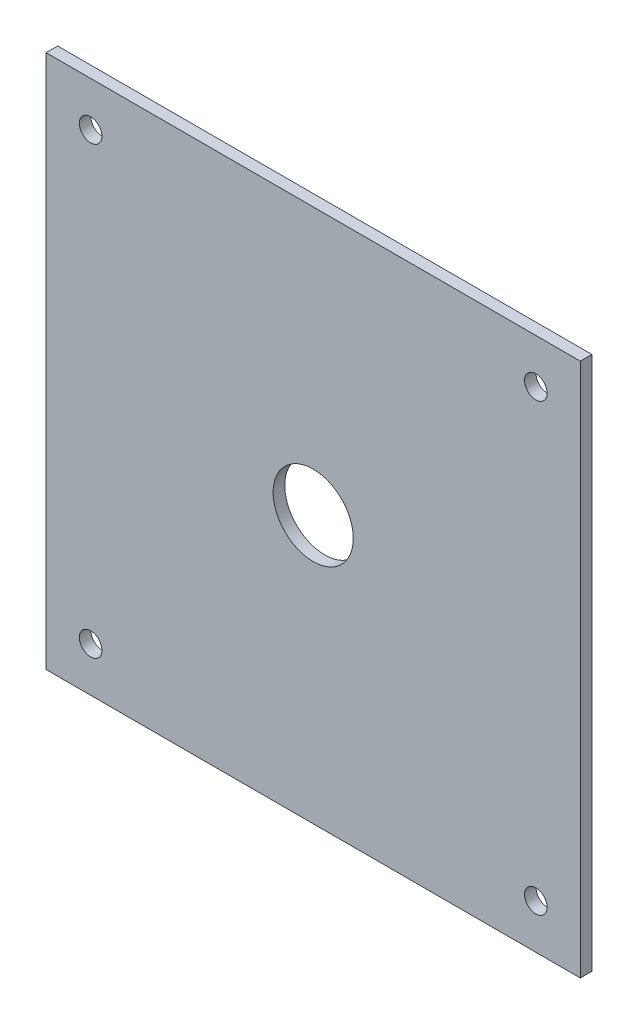
SolidWorks part; units mm, degrees
ref_plane "Front Plane" through (0, 0, 0) normal (0, 0, 1) x (1, 0, 0)
ref_plane "Top Plane" through (0, 0, 0) normal (0, 1, 0) x (1, 0, 0)
ref_plane "Right Plane" through (0, 0, 0) normal (1, 0, 0) x (0, 0, -1)
sketch "Sketch1" plane through (0, 0, 0) normal (0, 0, 1) x (1, 0, 0)
  line L0 (-181.1888, 0) -> (191.7786, 0) construction
  line L1 (-76.2, -76.2) -> (76.2, -76.2)
  line L2 (-76.2, -76.2) -> (-76.2, 76.2)
  line L3 (-76.2, 76.2) -> (76.2, 76.2)
  line L4 (76.2, -76.2) -> (76.2, 76.2)
  line L5 (-76.2, -76.2) -> (76.2, 76.2) construction
  line L6 (-76.2, 76.2) -> (76.2, -76.2) construction
  line L7 (0, 161.9694) -> (0, -107.8581) construction
  circle A0 centre (0, 0) radius 11.43
  circle A2 centre (-63.5, 63.5) radius 3.2258
  circle A3 centre (63.5, 63.5) radius 3.2258
  circle A4 centre (63.5, -63.5) radius 3.2258
  circle A5 centre (-63.5, -63.5) radius 3.2258
  point P0 (0, 0)
  dimension "D3" = 22.86
  dimension "D6" = 6.4516
  dimension "D7" = 12.7
  dimension "D1" = 152.4
  dimension "D2" = 152.4
  dimension "D4" = 76.2
  dimension "D5" = 76.2
  dimension "D8" = 12.7
extrude "Boss-Extrude1" add sketch "Sketch1" along normal blind 3.302
